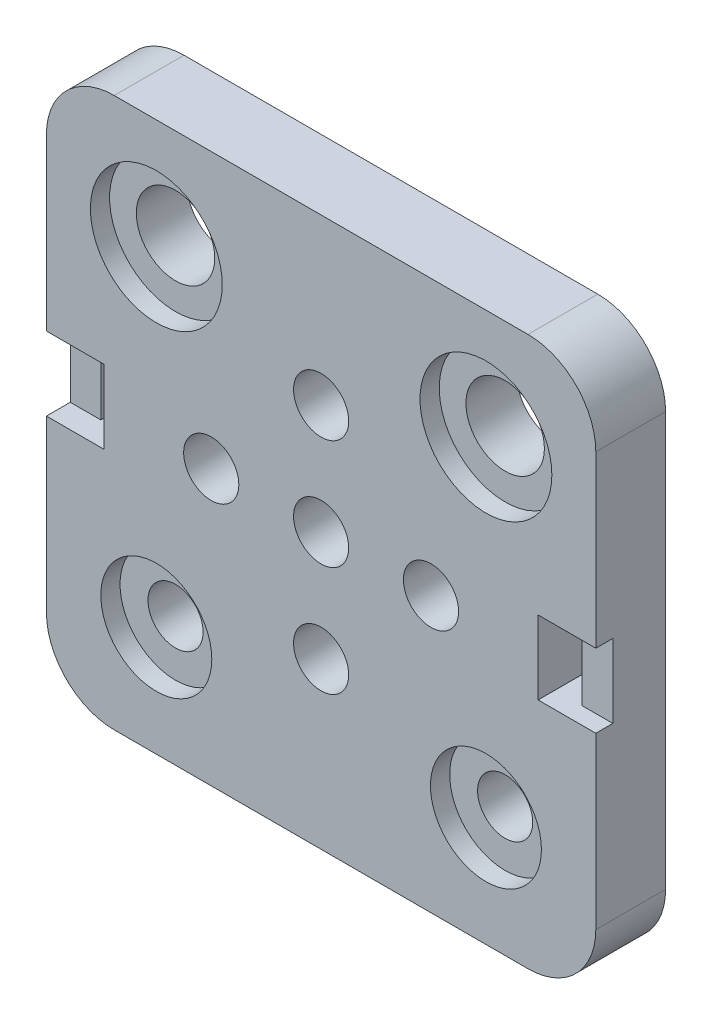
SolidWorks part; units mm, degrees
ref_plane "Front Plane" through (0, 0, 0) normal (0, 0, 1) x (1, 0, 0)
ref_plane "Top Plane" through (0, 0, 0) normal (0, 1, 0) x (1, 0, 0)
ref_plane "Right Plane" through (0, 0, 0) normal (1, 0, 0) x (0, 0, -1)
sketch "Sketch1" plane through (0, 0, 0) normal (0, 0, 1) x (1, 0, 0)
  line L0 (0, 25) -> (0, -25) construction
  line L1 (-25, 25) -> (25, 25)
  line L2 (-25, 25) -> (-25, -25)
  line L3 (-25, -25) -> (25, -25)
  line L4 (25, 25) -> (25, -25)
  line L5 (-25, 25) -> (25, -25) construction
  line L6 (-25, -25) -> (25, 25) construction
  line L7 (-15, 15) -> (15, 15) construction
  line L8 (-15, 15) -> (-15, -15) construction
  line L9 (-15, -15) -> (15, -15) construction
  line L10 (15, 15) -> (15, -15) construction
  line L11 (-15, 15) -> (15, -15) construction
  line L12 (-15, -15) -> (15, 15) construction
  line L14 (-25, 0) -> (25, 0) construction
  line L15 (-10, 10) -> (10, 10) construction
  line L16 (-10, 10) -> (-10, -10) construction
  line L17 (-10, -10) -> (10, -10) construction
  line L18 (10, 10) -> (10, -10) construction
  line L19 (-10, 10) -> (10, -10) construction
  line L20 (-10, -10) -> (10, 10) construction
  circle A0 centre (-15, 15) radius 3.57
  circle A1 centre (15, 15) radius 3.57
  circle A2 centre (15, -15) radius 2.51
  circle A3 centre (-15, -15) radius 2.51
  circle A4 centre (-10, 0) radius 2.51
  circle A5 centre (0, 10) radius 2.51
  circle A6 centre (10, 0) radius 2.51
  circle A7 centre (0, -10) radius 2.51
  circle A8 centre (0, 0) radius 2.51
  point P0 (0, 0)
  point P6 (0, 0)
  point P19 (0, 0)
  dimension "D4" = 7.14
  dimension "D6" = 5.02
  dimension "D7" = 5.02
  dimension "D1" = 50
  dimension "D2" = 50
  dimension "D3" = 30
  dimension "D5" = 20
extrude "Boss-Extrude1" add sketch "Sketch1" along normal blind 6.35
sketch "Sketch2" plane through (0, 0, 6.35) normal (0, 0, 1) x (1, 0, 0)
  circle A5 centre (-15, 15) radius 6
  circle A6 centre (-15, 15) radius 6
  circle A8 centre (15, 15) radius 6
  circle A9 centre (15, 15) radius 6
  circle A11 centre (-15, -15) radius 5.05
  circle A12 centre (-15, -15) radius 5.05
  circle A14 centre (15, -15) radius 5.05
  circle A15 centre (15, -15) radius 5.05
  dimension "D1" = 2.43
  dimension "D2" = 2.43
  dimension "D3" = 2.54
  dimension "D4" = 2.54
extrude "Cut-Extrude1" cut sketch "Sketch2" against normal blind 1.75
sketch "Sketch3" plane through (0, 0, 6.35) normal (0, 0, 1) x (1, 0, 0)
  line L0 (-25, 25) -> (-25, -25) construction
  line L1 (-25, 3.35) -> (-19.75, 3.35)
  line L2 (-25, 3.35) -> (-25, -3.35)
  line L3 (-25, -3.35) -> (-19.75, -3.35)
  line L4 (-19.75, 3.35) -> (-19.75, -3.35)
  line L5 (-25, 25) -> (-25, -25) construction
  line L6 (-25, 0) -> (25, 0) construction
  line L7 (25, -25) -> (25, 25) construction
  line L8 (0, 25) -> (0, -25) construction
  line L9 (25, 25) -> (-25, 25) construction
  line L10 (-25, -25) -> (25, -25) construction
  line L11 (19.75, 3.35) -> (19.75, -3.35)
  line L12 (25, -3.35) -> (19.75, -3.35)
  line L13 (25, 3.35) -> (25, -3.35)
  line L14 (25, 3.35) -> (19.75, 3.35)
  point P8 (-25, 0)
  point P9 (-25, 0)
  dimension "D1" = 5.25
  dimension "D2" = 6.7
extrude "Cut-Extrude2" cut sketch "Sketch3" against normal blind 7
sketch "Sketch4" plane through (0, 3.35, 0) normal (0, -1, 0) x (1, 0, 0)
  line L1 (-25, 0) -> (-22.215, 0)
  line L2 (-25, 0) -> (-25, 4.18)
  line L3 (-25, 4.18) -> (-22.215, 4.18)
  line L4 (-22.215, 0) -> (-22.215, 4.18)
  line L5 (25, 0) -> (22.21, 0)
  line L6 (25, 0) -> (25, 4.8)
  line L7 (25, 4.8) -> (22.21, 4.8)
  line L8 (22.21, 0) -> (22.21, 4.8)
  dimension "D1" = 4.18
  dimension "D2" = 2.785
  dimension "D3" = 4.8
  dimension "D4" = 2.79
extrude "Boss-Extrude3" add sketch "Sketch4" along normal up to surface (6.7 mm away) up to face at (-22.375, -3.35, 3.175)
fillet "Fillet1" radius 6.17 4 edges at (-25, -25, 3.175) (25, -25, 3.175) (25, 25, 3.175) (-25, 25, 3.175)
